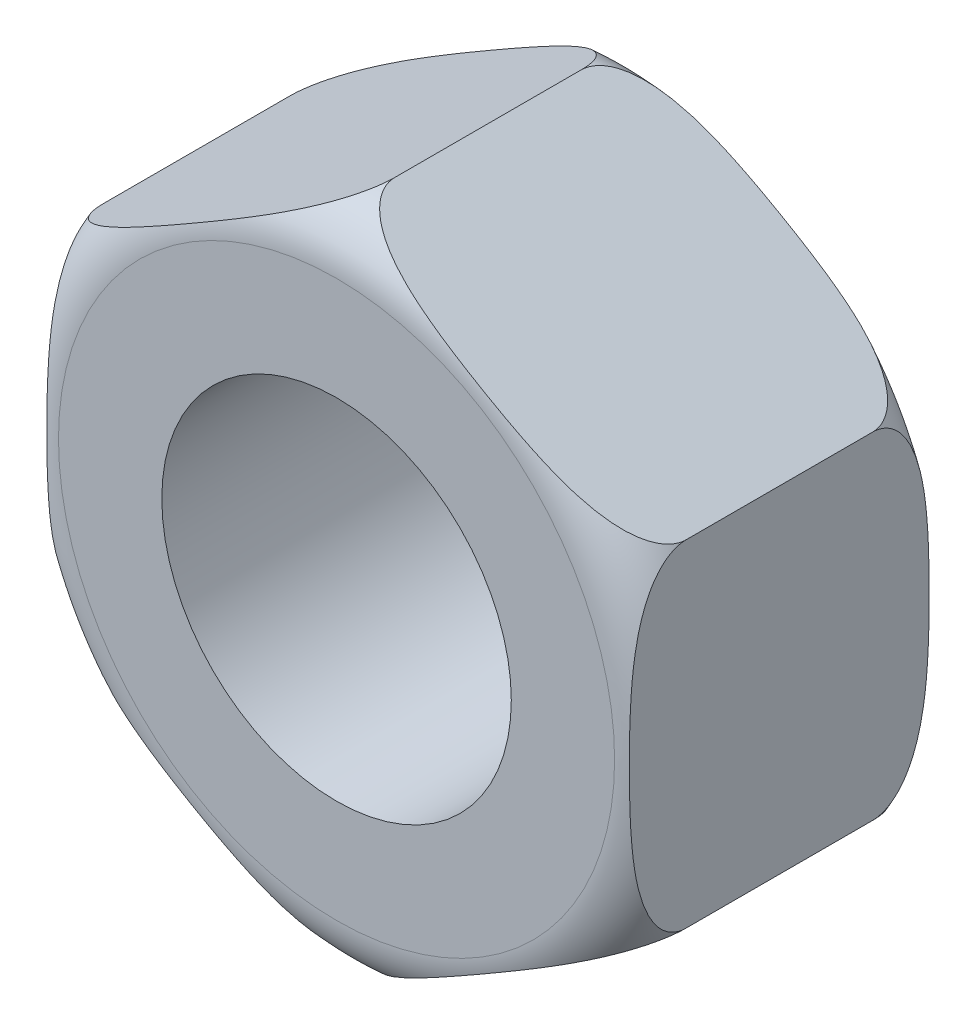
SolidWorks part; units mm, degrees
ref_plane "Plane1" through (0, 0, 0) normal (0, 0, 1) x (1, 0, 0)
ref_plane "Plane2" through (0, 0, 0) normal (0, 1, 0) x (-1, 0, 0)
ref_plane "Plane3" through (0, 0, 0) normal (1, 0, 0) x (0, 0, -1)
sketch "Head Sketch" plane through (0, 0, 0) normal (0, 0, 1) x (1, 0, 0)
  line L0 (0, 5.7735) -> (5, 2.8868)
  line L1 (5, 2.8868) -> (5, -2.8868)
  line L2 (5, -2.8868) -> (0, -5.7735)
  line L3 (0, -5.7735) -> (-5, -2.8868)
  line L4 (-5, -2.8868) -> (-5, 2.8868)
  line L5 (-5, 2.8868) -> (0, 5.7735)
  line L6 (5, 2.8868) -> (-5, -2.8868) construction
  line L7 (0, 5.7735) -> (0, -5.7735) construction
  line L8 (-5, 2.8868) -> (5, -2.8868) construction
  point P0 (0, 0)
  dimension "D1" = 60
  dimension "D2" = 60
  dimension "Flats" = 10
extrude "Head" add sketch "Head Sketch" along normal blind 5.2
sketch "Sketch5" plane through (0, 0, 0) normal (1, 0, 0) x (0, 0, -1)
  line L0 (-5.2, -4.7735) -> (-5.2, -5.7735)
  line L1 (-5.2, -5.7735) -> (-4.2, -5.7735)
  line L2 (-5.2, -5.7735) -> (0, -5.7735) construction
  line L3 (-5.2, -5.7735) -> (-5.2, -2.8868) construction
  line L5 (-15.0856, 0) -> (-8.1394, 0) construction
  line L6 (50, 0) -> (-50, 0) construction
  arc A0 (-5.2, -4.7735) -> (-4.2, -5.7735) centre (-4.2, -4.7735) ccw
  dimension "D1" = 1
revolve "Head Trim" cut sketch "Sketch5" angle 360 about L5
sketch "Hole Sketch" plane through (0, 0, 5.2) normal (0, 0, 1) x (1, 0, 0)
  line L0 (50, 0) -> (-50, 0) construction
  line L1 (0, -50) -> (0, 50) construction
  circle A0 centre (0, 0) radius 3
  dimension "Hole Dia" = 6
extrude "Through Hole" cut sketch "Hole Sketch" against normal through all
cosmetic thread "Cosmetic Thread1" parameters "D2"=7
ref_plane "Plan1" through (0, 0, 2.6) normal (0, 0, 1) x (1, 0, 0)
mirror "Symétrie2" about plane through (0, 0, 2.6) normal (0, 0, 1)
